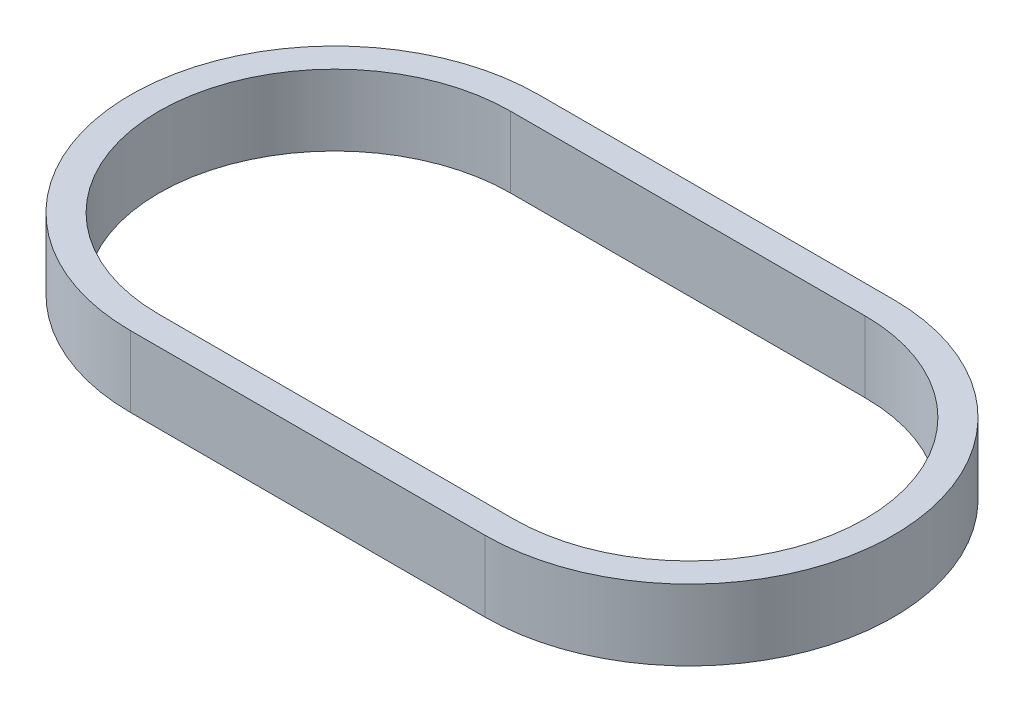
SolidWorks part; units mm, degrees
ref_plane "Front Plane" through (0, 0, 0) normal (0, 0, 1) x (1, 0, 0)
ref_plane "Top Plane" through (0, 0, 0) normal (0, 1, 0) x (1, 0, 0)
ref_plane "Right Plane" through (0, 0, 0) normal (1, 0, 0) x (0, 0, -1)
sketch "Sketch1" plane through (0, 0, 0) normal (0, 1, 0) x (1, 0, 0)
  line L0 (0, 0) -> (25, 0) construction
  line L1 (0, 12.4) -> (25, 12.4)
  line L2 (0, -12.4) -> (25, -12.4)
  line L3 (0, 0) -> (25, 0) construction
  line L4 (0, 14.4) -> (25, 14.4)
  line L5 (0, -14.4) -> (25, -14.4)
  arc A0 (0, 12.4) -> (0, -12.4) centre (0, 0) ccw
  arc A1 (25, -12.4) -> (25, 12.4) centre (25, 0) ccw
  arc A2 (0, 14.4) -> (0, -14.4) centre (0, 0) ccw
  arc A3 (25, -14.4) -> (25, 14.4) centre (25, 0) ccw
  point P3 (12.5, 0)
  point P10 (12.5, 0)
  dimension "D1" = 24.8
  dimension "D2" = 25
  dimension "D3" = 2
extrude "Boss-Extrude1" add sketch "Sketch1" along normal blind 5
